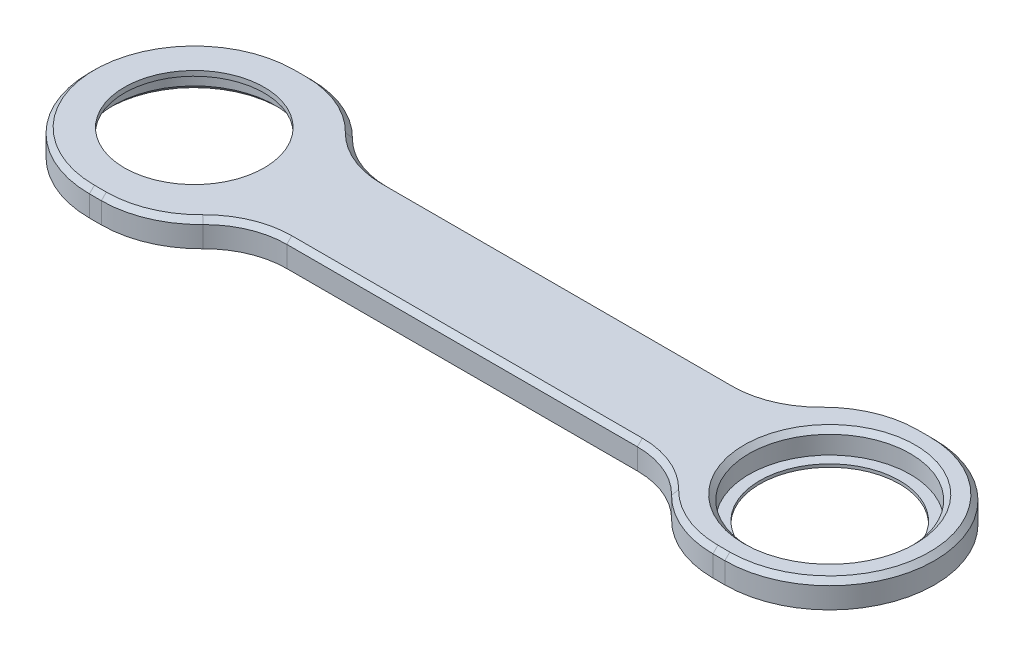
SolidWorks part; units mm, degrees
ref_plane "Front Plane" through (0, 0, 0) normal (0, 0, 1) x (1, 0, 0)
ref_plane "Top Plane" through (0, 0, 0) normal (0, 1, 0) x (1, 0, 0)
ref_plane "Right Plane" through (0, 0, 0) normal (1, 0, 0) x (0, 0, -1)
sketch "Sketch1" plane through (0, 0, 0) normal (0, 1, 0) x (1, 0, 0)
  line L0 (63.625, 0) -> (-63.625, 0) construction
  line L1 (63.625, -21) -> (-63.625, -21)
  line L2 (63.625, 21) -> (-63.625, 21)
  line L3 (-35.1066, 26.5458) -> (35.1066, 26.5458) construction
  line L4 (-35.1066, 43.0915) -> (35.1066, 43.0915)
  line L5 (-35.1066, 10) -> (35.1066, 10)
  line L6 (-35.1066, -26.5458) -> (35.1066, -26.5458) construction
  line L7 (-35.1066, -10) -> (35.1066, -10)
  line L8 (-35.1066, -43.0915) -> (35.1066, -43.0915)
  arc A0 (63.625, -21) -> (63.625, 21) centre (63.625, 0) ccw
  arc A1 (-63.625, 21) -> (-63.625, -21) centre (-63.625, 0) ccw
  circle A2 centre (-63.625, 0) radius 16.15
  arc A3 (-35.1066, 43.0915) -> (-35.1066, 10) centre (-35.1066, 26.5458) ccw
  arc A4 (35.1066, 10) -> (35.1066, 43.0915) centre (35.1066, 26.5458) ccw
  arc A5 (-35.1066, -10) -> (-35.1066, -43.0915) centre (-35.1066, -26.5458) ccw
  arc A6 (35.1066, -43.0915) -> (35.1066, -10) centre (35.1066, -26.5458) ccw
  circle A7 centre (63.625, 0) radius 16.15
  point P2 (0, 0)
  point P12 (0, 26.5458)
  point P19 (0, -26.5458)
  dimension "D2" = 32.3
  dimension "D3" = 21
  dimension "D6" = 32.3
  dimension "D1" = 127.25
  dimension "D4" = 10
  dimension "D5" = 10
extrude "Boss-Extrude1" add sketch "Sketch1" along normal blind 5.2 contours A6 L1 A0 L2 A4 L5 A3 A1 A5 L7 A7 A2
fillet "Fillet1" radius 20 4 edges at (50.6953, 2.6, 21) (50.6953, 2.6, -21) (-50.6953, 2.6, -21) (-50.6953, 2.6, 21)
chamfer "Chamfer1" distance 1 angle 45 17 edges at (63.625, 5.2, 16.15) (0, 5.2, -10) (-41.5253, 5.2, -11.2958) (41.5253, 5.2, -11.2958) (-62.433, 5.2, -21) (62.433, 5.2, -21) (-84.625, 5.2, 0) (84.625, 5.2, 0) (-62.433, 5.2, 21) (62.433, 5.2, 21) (-41.5253, 5.2, 11.2958) (41.5253, 5.2, 11.2958) (0, 5.2, 10) (-53.4822, 5.2, -19.4337) (53.4822, 5.2, -19.4337) (-53.4822, 5.2, 19.4337) (53.4822, 5.2, 19.4337)
sketch "Sketch2" plane through (0, 0, 0) normal (0, -1, 0) x (1, 0, 0)
  circle A2 centre (63.625, 0) radius 14
  circle A3 centre (63.625, 0) radius 19.0252
  dimension "D2" = 28
extrude "Boss-Extrude2" add sketch "Sketch2" against normal blind 0.6
sketch "Sketch3" plane through (0, 5.2, 0) normal (0, 1, 0) x (1, 0, 0)
  line L0 (77.77, 28.8659) -> (77.77, -26.5149) construction
  line L1 (0, 0) -> (86.87, 0) construction
  line L2 (79.775, 17.2779) -> (79.775, -15.919) construction
  circle A1 centre (63.625, 0) radius 16.15 construction
  dimension "D1" = 86.87
  dimension "D2" = 9.1
sketch "Sketch4" plane through (0, 5.2, 0) normal (0, 1, 0) x (1, 0, 0)
  circle A0 centre (-63.625, 0) radius 18.7153
  circle A1 centre (-63.625, 0) radius 14
  dimension "D1" = 28
extrude "Boss-Extrude3" add sketch "Sketch4" against normal blind 1
chamfer "Chamfer2" distance 1 angle 45 1 edges at (-63.625, 0, 16.15)
